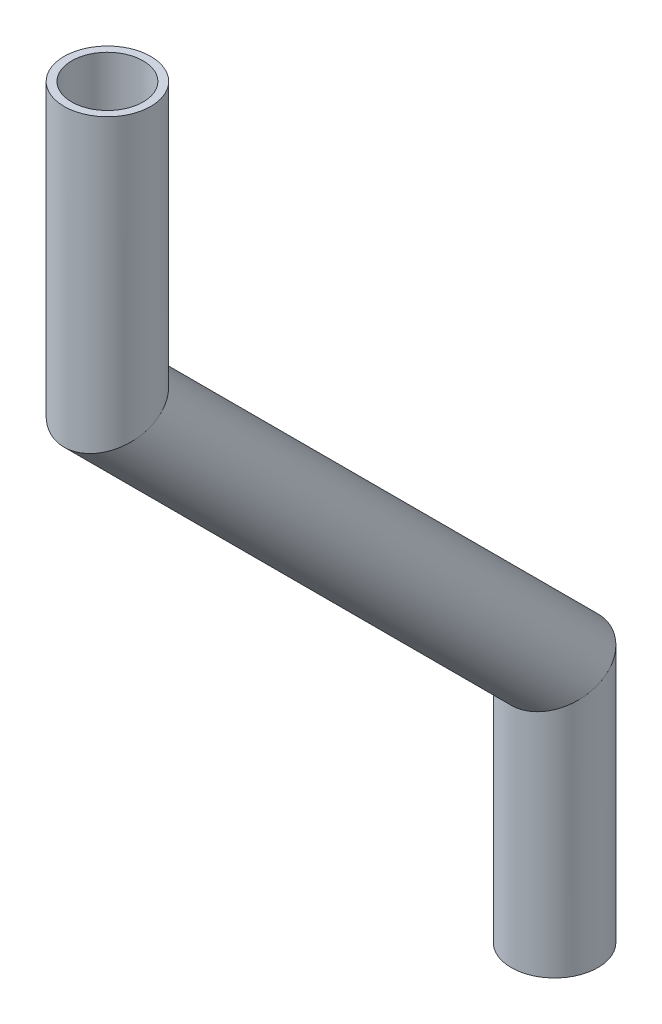
SolidWorks part; units mm, degrees
ref_plane "Front Plane" through (0, 0, 0) normal (0, 0, 1) x (1, 0, 0)
ref_plane "Top Plane" through (0, 0, 0) normal (0, 1, 0) x (1, 0, 0)
ref_plane "Right Plane" through (0, 0, 0) normal (1, 0, 0) x (0, 0, -1)
sketch "Sketch1" plane through (0, 0, 0) normal (1, 0, 0) x (0, 0, -1)
  line L0 (-599.141, 1553.9035) -> (-599.141, 1571.8588)
  line L1 (-599.141, 1571.8588) -> (-631.8973, 1604.615)
  line L2 (-631.8973, 1604.615) -> (-631.8973, 1624.9183)
  line L3 (-599.141, 1571.8588) -> (-599.141, 1599.544) construction
  point P4 (-631.8973, 1624.9183)
  point P6 (0, 0)
  dimension "D1" = 45
other "Pipe 0.5 SCH 40(1)"
ref_plane "Plane1" through (0, 1571.8588, 599.141) normal (0, 0.7071, 0.7071) x (0, -0.7071, 0.7071)
sketch "Sketch11" plane through (0, 1571.8588, 599.141) normal (0, 0.7071, 0.7071) x (0, -0.7071, 0.7071)
  circle A0 centre (0, 0) radius 2.6162
  circle A1 centre (0, 0) radius 3.175
  point P5 (0, 0)
  dimension "In_dia" = 5.2324
  dimension "Out_dia" = 6.35
